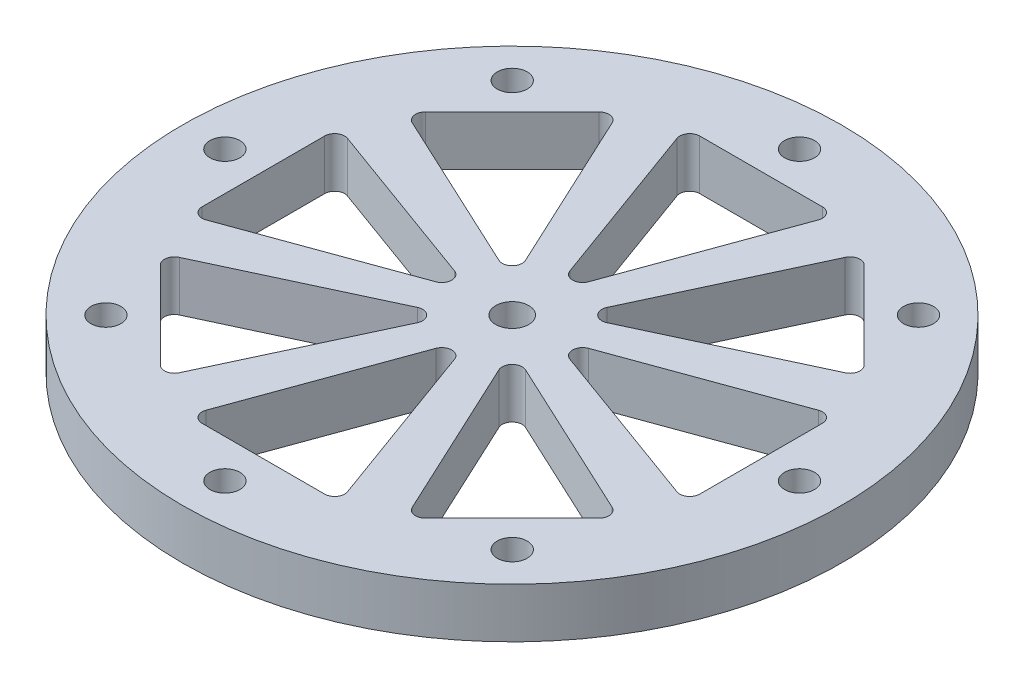
SolidWorks part; units mm, degrees
ref_plane "Front Plane" through (0, 0, 0) normal (0, 0, 1) x (1, 0, 0)
ref_plane "Top Plane" through (0, 0, 0) normal (0, 1, 0) x (1, 0, 0)
ref_plane "Right Plane" through (0, 0, 0) normal (1, 0, 0) x (0, 0, -1)
sketch "Sketch1" plane through (0, 0, 0) normal (0, 1, 0) x (1, 0, 0)
  circle A0 centre (0, 0) radius 1.65
  circle A1 centre (0, -0.021) radius 33
  dimension "D1" = 3.3
  dimension "D2" = 66
extrude "Boss-Extrude1" add sketch "Sketch1" along normal blind 5
sketch "Sketch2" plane through (0, 5, 0) normal (0, 1, 0) x (1, 0, 0)
  line L0 (0, 0) -> (0, 23.3421) construction
  line L1 (-0.9397, 6.71) -> (-7.078, 23.5749)
  line L2 (0.9397, 6.71) -> (7.078, 23.5749)
  line L3 (-6.1383, 24.9169) -> (6.1383, 24.9169)
  line L4 (13.2785, 21.9594) -> (21.9594, 13.2785)
  line L5 (5.4091, 4.0802) -> (21.6749, 11.6651)
  line L6 (4.0802, 5.4091) -> (11.6651, 21.6749)
  line L7 (24.9169, 6.1383) -> (24.9169, -6.1383)
  line L8 (6.71, -0.9397) -> (23.5749, -7.078)
  line L9 (6.71, 0.9397) -> (23.5749, 7.078)
  line L10 (21.9594, -13.2785) -> (13.2785, -21.9594)
  line L11 (4.0802, -5.4091) -> (11.6651, -21.6749)
  line L12 (5.4091, -4.0802) -> (21.6749, -11.6651)
  line L13 (6.1383, -24.9169) -> (-6.1383, -24.9169)
  line L14 (-0.9397, -6.71) -> (-7.078, -23.5749)
  line L15 (0.9397, -6.71) -> (7.078, -23.5749)
  line L16 (-13.2785, -21.9594) -> (-21.9594, -13.2785)
  line L17 (-5.4091, -4.0802) -> (-21.6749, -11.6651)
  line L18 (-4.0802, -5.4091) -> (-11.6651, -21.6749)
  line L19 (-24.9169, -6.1383) -> (-24.9169, 6.1383)
  line L20 (-6.71, 0.9397) -> (-23.5749, 7.078)
  line L21 (-6.71, -0.9397) -> (-23.5749, -7.078)
  line L22 (-21.9594, 13.2785) -> (-13.2785, 21.9594)
  line L23 (-4.0802, 5.4091) -> (-11.6651, 21.6749)
  line L24 (-5.4091, 4.0802) -> (-21.6749, 11.6651)
  circle A0 centre (0, 0) radius 4.0879 construction
  arc A1 (-0.9397, 6.71) -> (0.9397, 6.71) centre (0, 7.052) ccw
  arc A2 (7.078, 23.5749) -> (6.1383, 24.9169) centre (6.1383, 23.9169) ccw
  arc A3 (-7.078, 23.5749) -> (-6.1383, 24.9169) centre (-6.1383, 23.9169) cw
  arc A4 (11.6651, 21.6749) -> (13.2785, 21.9594) centre (12.5714, 21.2523) cw
  arc A5 (21.6749, 11.6651) -> (21.9594, 13.2785) centre (21.2523, 12.5714) ccw
  arc A6 (4.0802, 5.4091) -> (5.4091, 4.0802) centre (4.9865, 4.9865) ccw
  arc A7 (23.5749, 7.078) -> (24.9169, 6.1383) centre (23.9169, 6.1383) cw
  arc A8 (23.5749, -7.078) -> (24.9169, -6.1383) centre (23.9169, -6.1383) ccw
  arc A9 (6.71, 0.9397) -> (6.71, -0.9397) centre (7.052, 0) ccw
  arc A10 (21.6749, -11.6651) -> (21.9594, -13.2785) centre (21.2523, -12.5714) cw
  arc A11 (11.6651, -21.6749) -> (13.2785, -21.9594) centre (12.5714, -21.2523) ccw
  arc A12 (5.4091, -4.0802) -> (4.0802, -5.4091) centre (4.9865, -4.9865) ccw
  arc A13 (7.078, -23.5749) -> (6.1383, -24.9169) centre (6.1383, -23.9169) cw
  arc A14 (-7.078, -23.5749) -> (-6.1383, -24.9169) centre (-6.1383, -23.9169) ccw
  arc A15 (0.9397, -6.71) -> (-0.9397, -6.71) centre (0, -7.052) ccw
  arc A16 (-11.6651, -21.6749) -> (-13.2785, -21.9594) centre (-12.5714, -21.2523) cw
  arc A17 (-21.6749, -11.6651) -> (-21.9594, -13.2785) centre (-21.2523, -12.5714) ccw
  arc A18 (-4.0802, -5.4091) -> (-5.4091, -4.0802) centre (-4.9865, -4.9865) ccw
  arc A19 (-23.5749, -7.078) -> (-24.9169, -6.1383) centre (-23.9169, -6.1383) cw
  arc A20 (-23.5749, 7.078) -> (-24.9169, 6.1383) centre (-23.9169, 6.1383) ccw
  arc A21 (-6.71, -0.9397) -> (-6.71, 0.9397) centre (-7.052, 0) ccw
  arc A22 (-21.6749, 11.6651) -> (-21.9594, 13.2785) centre (-21.2523, 12.5714) cw
  arc A23 (-11.6651, 21.6749) -> (-13.2785, 21.9594) centre (-12.5714, 21.2523) ccw
  arc A24 (-5.4091, 4.0802) -> (-4.0802, 5.4091) centre (-4.9865, 4.9865) ccw
  point P9 (0, 4.1282)
  point P12 (7.5665, 24.9169)
  point P15 (-7.5665, 24.9169)
  point P82 (0, 0)
  dimension "D2" = 1
  dimension "D1" = 20
  dimension "D3" = 8
extrude "Cut-Extrude2" cut sketch "Sketch2" against normal through all contours A3 L1 A1 L2 A2 L3 | L6 A6 L5 A5 L4 A4 | L9 A9 L8 A8 L7 A7 | L12 A12 L11 A11 L10 A10 | L15 A15 L14 A14 L13 A13 | L18 A18 L17 A17 L16 A16 | L21 A21 L20 A20 L19 A19 | L24 A24 L23 A23 L22 A22
sketch "Sketch3" plane through (0, 5, 0) normal (0, 1, 0) x (1, 0, 0)
  line L0 (0, 0) -> (0, 28.7697) construction
  circle A0 centre (0, 28.7697) radius 1.5
  circle A1 centre (20.3433, 20.3433) radius 1.5
  circle A2 centre (28.7697, 0) radius 1.5
  circle A3 centre (20.3433, -20.3433) radius 1.5
  circle A4 centre (0, -28.7697) radius 1.5
  circle A5 centre (-20.3433, -20.3433) radius 1.5
  circle A6 centre (-28.7697, 0) radius 1.5
  circle A7 centre (-20.3433, 20.3433) radius 1.5
  point P21 (0, 0)
  dimension "D1" = 3
  dimension "D2" = 8
extrude "Cut-Extrude3" cut sketch "Sketch3" against normal through all
